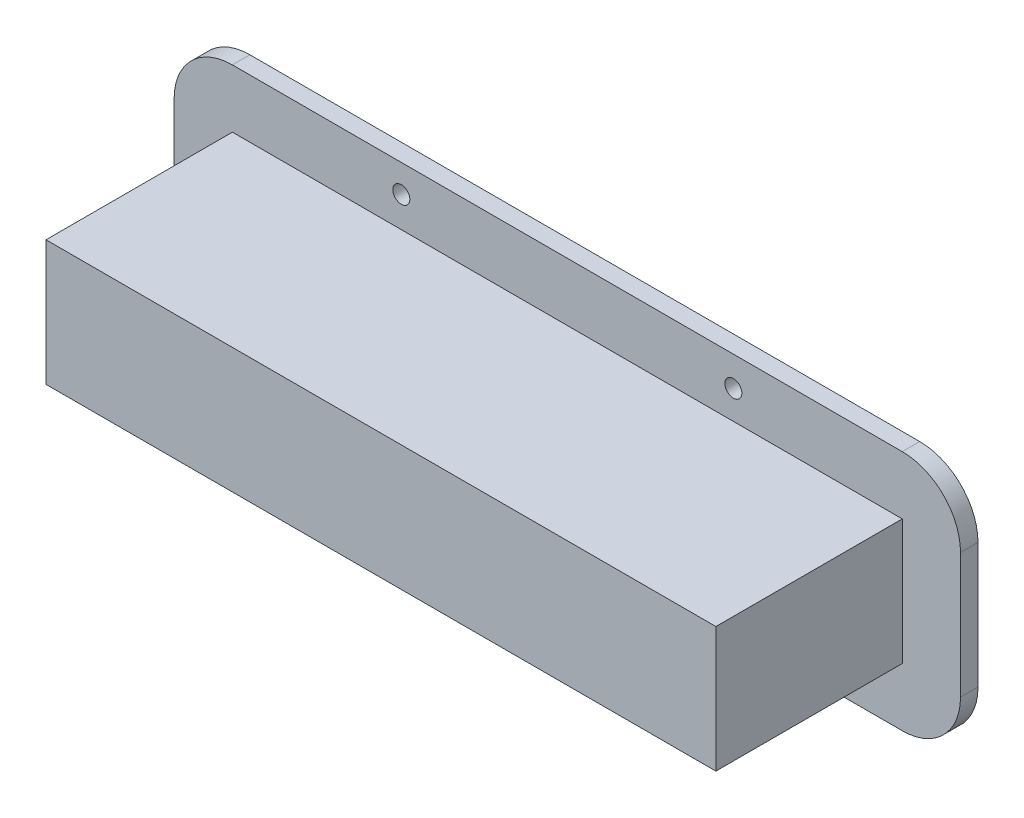
SolidWorks part; units mm, degrees
ref_plane "Front Plane" through (0, 0, 0) normal (0, 0, 1) x (1, 0, 0)
ref_plane "Top Plane" through (0, 0, 0) normal (0, 1, 0) x (1, 0, 0)
ref_plane "Right Plane" through (0, 0, 0) normal (1, 0, 0) x (0, 0, -1)
sketch "Sketch2" plane through (0, 0, 0) normal (0, 0, 1) x (1, 0, 0)
  line L1 (-47.7147, 9.7714) -> (67.2853, 9.7714)
  line L2 (-47.7147, 9.7714) -> (-47.7147, -11.7286)
  line L3 (-47.7147, -11.7286) -> (67.2853, -11.7286)
  line L4 (67.2853, 9.7714) -> (67.2853, -11.7286)
  dimension "D1" = 115
  dimension "D2" = 21.5
extrude "Boss-Extrude1" add sketch "Sketch2" along normal blind 35
sketch "Sketch7" plane through (0, 0, 0) normal (0, 0, 1) x (1, 0, 0)
  line L0 (-47.7147, 9.7714) -> (-47.7147, -11.7286) construction
  line L1 (-47.7147, 19.7714) -> (67.2853, 19.7714)
  line L2 (-57.7147, 9.7714) -> (-57.7147, -11.7286)
  line L3 (-47.7147, -21.7286) -> (67.2853, -21.7286)
  line L4 (77.2853, 9.7714) -> (77.2853, -11.7286)
  line L5 (67.2853, -11.7286) -> (67.2853, 9.7714) construction
  line L6 (67.2853, 9.7714) -> (-47.7147, 9.7714) construction
  line L7 (-47.7147, -11.7286) -> (67.2853, -11.7286) construction
  arc A0 (-47.7147, 19.7714) -> (-57.7147, 9.7714) centre (-47.7147, 9.7714) ccw
  arc A1 (-57.7147, -11.7286) -> (-47.7147, -21.7286) centre (-47.7147, -11.7286) ccw
  arc A2 (77.2853, -11.7286) -> (67.2853, -21.7286) centre (67.2853, -11.7286) cw
  arc A3 (67.2853, 19.7714) -> (77.2853, 9.7714) centre (67.2853, 9.7714) cw
  dimension "D5" = 10
  dimension "D6" = 10
  dimension "D1" = 10
  dimension "D2" = 10
  dimension "D3" = 10
  dimension "D4" = 10
extrude "Boss-Extrude2" add sketch "Sketch7" along normal blind 3
sketch "Sketch8" plane through (0, 0, 0) normal (0, 0, 1) x (1, 0, 0)
  line L0 (77.2853, -11.7286) -> (77.2853, 9.7714) construction
  line L1 (62.2853, 4.7714) -> (-42.7147, 4.7714)
  line L2 (62.2853, 4.7714) -> (62.2853, -6.7286)
  line L3 (62.2853, -6.7286) -> (-42.7147, -6.7286)
  line L4 (-42.7147, 4.7714) -> (-42.7147, -6.7286)
  line L6 (-57.7147, 9.7714) -> (-57.7147, -11.7286) construction
  line L7 (67.2853, 19.7714) -> (-47.7147, 19.7714) construction
  line L8 (-47.7147, -21.7286) -> (67.2853, -21.7286) construction
  dimension "D1" = 15
  dimension "D2" = 15
  dimension "D3" = 15
  dimension "D4" = 15
extrude "Cut-Extrude2" cut sketch "Sketch8" along normal blind 30
sketch "Sketch9" plane through (0, 0, 0) normal (0, 0, 1) x (1, 0, 0)
  circle A0 centre (38.2853, 14.6854) radius 1.46
  circle A1 centre (-18.7147, 15.0074) radius 1.46
  circle A2 centre (-18.7147, -16.3426) radius 1.46
  circle A3 centre (38.2853, -16.6646) radius 1.46
  dimension "D1" = 31.35
  dimension "D2" = 57
  dimension "D6" = 31.35
extrude "Cut-Extrude3" cut sketch "Sketch9" along normal blind 33
sketch "Sketch10" plane through (0, 0, 0) normal (1, 0, 0) x (0, 0, -1)
  line L1 (-11.5, 3.2714) -> (-26.5, 3.2714)
  line L2 (-11.5, 3.2714) -> (-11.5, -5.2286)
  line L3 (-11.5, -5.2286) -> (-26.5, -5.2286)
  line L4 (-26.5, 3.2714) -> (-26.5, -5.2286)
extrude "Cut-Extrude4" cut sketch "Sketch10" against normal blind 88
